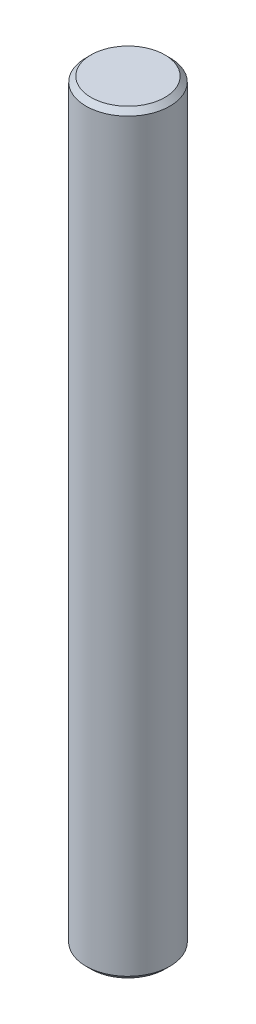
SolidWorks part; units mm, degrees
ref_plane "Спереди" through (0, 0, 0) normal (0, 0, 1) x (1, 0, 0)
ref_plane "Сверху" through (0, 0, 0) normal (0, 1, 0) x (1, 0, 0)
ref_plane "Справа" through (0, 0, 0) normal (1, 0, 0) x (0, 0, -1)
sketch "Эскиз1" plane through (0, 0, 0) normal (0, 1, 0) x (1, 0, 0)
  circle A0 centre (0, 0) radius 2.5
extrude "Бобышка-Вытянуть1" add sketch "Эскиз1" along normal blind 45
chamfer "Фаска1" distance 0.3 angle 45 2 edges at (0, 0, 2.5) (0, 45, 2.5)
